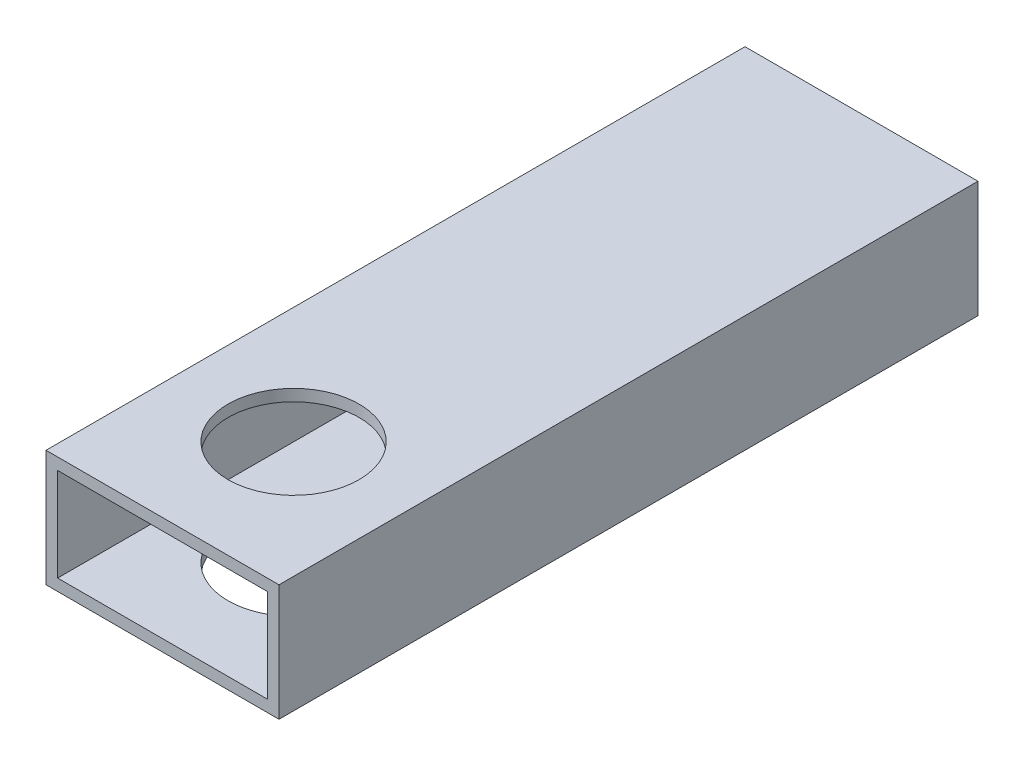
SolidWorks part; units mm, degrees
ref_plane "Front Plane" through (0, 0, 0) normal (0, 0, 1) x (1, 0, 0)
ref_plane "Top Plane" through (0, 0, 0) normal (0, 1, 0) x (1, 0, 0)
ref_plane "Right Plane" through (0, 0, 0) normal (1, 0, 0) x (0, 0, -1)
sketch "Sketch1" plane through (0, 0, 0) normal (0, 0, 1) x (1, 0, 0)
  line L0 (25.4, 0) -> (25.4, -2.54) construction
  line L1 (0, 0) -> (50.8, 0)
  line L2 (0, 0) -> (0, -25.4)
  line L3 (0, -25.4) -> (50.8, -25.4)
  line L4 (50.8, 0) -> (50.8, -25.4)
  line L5 (2.54, -2.54) -> (48.26, -2.54)
  line L6 (2.54, -2.54) -> (2.54, -22.86)
  line L7 (2.54, -22.86) -> (48.26, -22.86)
  line L8 (48.26, -2.54) -> (48.26, -22.86)
  line L9 (0, -12.7) -> (2.54, -12.7) construction
  dimension "D1" = 50.8
  dimension "D2" = 25.4
  dimension "D3" = 2.54
  dimension "D4" = 2.54
extrude "Boss-Extrude1" add sketch "Sketch1" along normal blind 152.4
sketch "Sketch2" plane through (0, 0, 0) normal (0, 1, 0) x (1, 0, 0)
  line L0 (25.4, -152.4) -> (25.4, -123.825) construction
  line L1 (50.8, -152.4) -> (0, -152.4) construction
  circle A0 centre (25.4, -123.825) radius 14.2875
  point P6 (0, 0)
  dimension "D1" = 28.575
  dimension "D2" = 28.575
extrude "Cut-Extrude1" cut sketch "Sketch2" against normal blind 152.4
